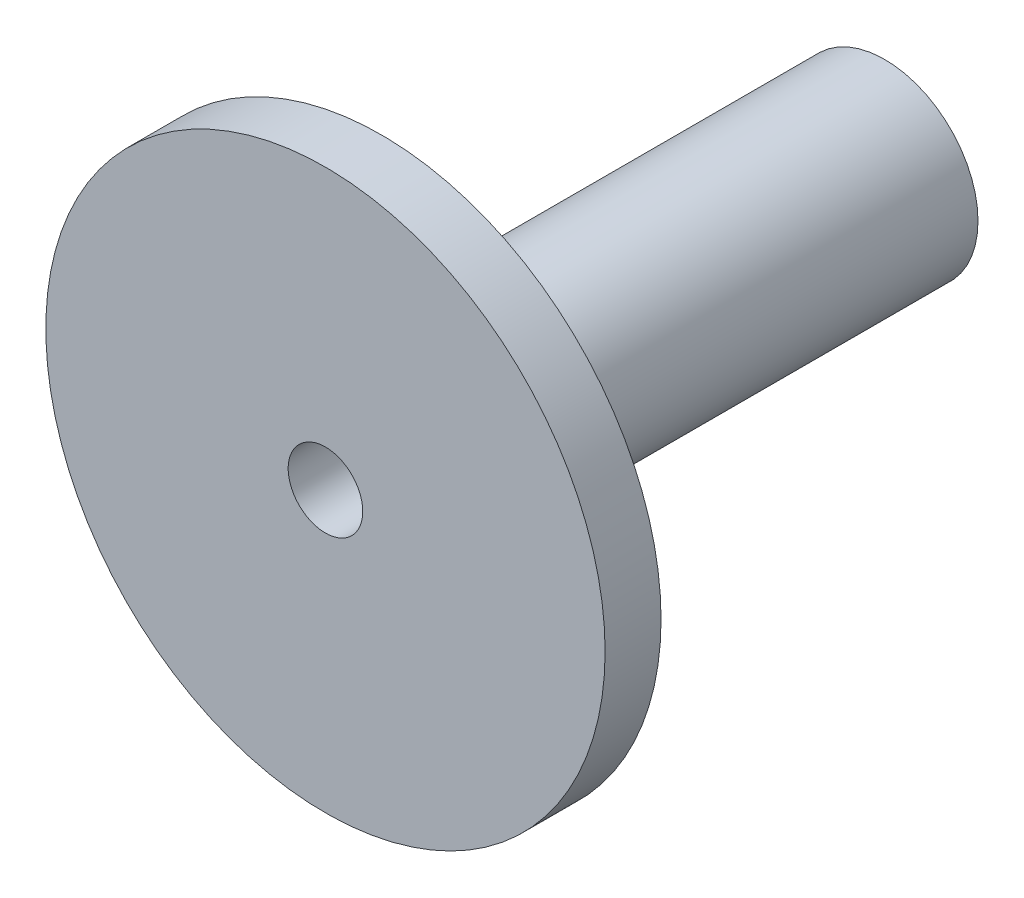
SolidWorks part; units mm, degrees
ref_plane "Front Plane" through (0, 0, 0) normal (0, 0, 1) x (1, 0, 0)
ref_plane "Top Plane" through (0, 0, 0) normal (0, 1, 0) x (1, 0, 0)
ref_plane "Right Plane" through (0, 0, 0) normal (1, 0, 0) x (0, 0, -1)
sketch "Sketch1" plane through (0, 0, 0) normal (0, 0, 1) x (1, 0, 0)
  circle A0 centre (0, 0) radius 5
  dimension "D1" = 10
extrude "Boss-Extrude1" add sketch "Sketch1" along normal blind 30
sketch "Sketch2" plane through (0, 0, 30) normal (0, 0, 1) x (1, 0, 0)
  circle A0 centre (0, 0) radius 2
  dimension "D1" = 4
extrude "Cut-Extrude1" cut sketch "Sketch2" against normal through all
sketch "Sketch4" plane through (0, 0, 30) normal (0, 0, 1) x (1, 0, 0)
  circle A0 centre (0, 0) radius 15
  circle M2 centre (0, 0) radius 5
  dimension "D1" = 30
extrude "Boss-Extrude3" add sketch "Sketch4" against normal blind 3 contours A0 M2
